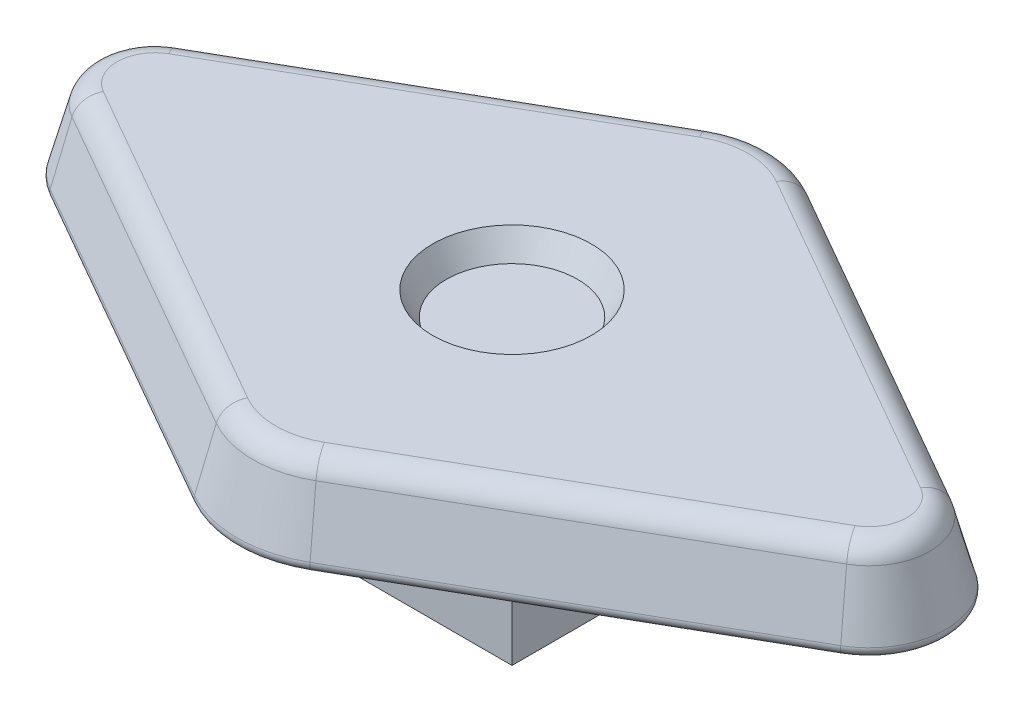
SolidWorks part; units mm, degrees
ref_plane "Front Plane" through (0, 0, 0) normal (0, 0, 1) x (1, 0, 0)
ref_plane "Top Plane" through (0, 0, 0) normal (0, 1, 0) x (1, 0, 0)
ref_plane "Right Plane" through (0, 0, 0) normal (1, 0, 0) x (0, 0, -1)
sketch "Sketch1" plane through (0, 0, 0) normal (0, 1, 0) x (1, 0, 0)
  line L1 (-1.27, -1.27) -> (1.27, -1.27)
  line L2 (-1.27, -1.27) -> (-1.27, 1.27)
  line L3 (-1.27, 1.27) -> (1.27, 1.27)
  line L4 (1.27, -1.27) -> (1.27, 1.27)
  line L5 (-1.27, -1.27) -> (1.27, 1.27) construction
  line L6 (-1.27, 1.27) -> (1.27, -1.27) construction
  point P0 (0, 0)
  dimension "D1" = 2.54
extrude "Boss-Extrude1" add sketch "Sketch1" along normal blind 2.54
sketch "Sketch2" plane through (0, 2.54, 0) normal (0, 1, 0) x (1, 0, 0)
  line L0 (-6.985, 0) -> (6.985, 0) construction
  line L1 (0, -4.445) -> (0, 4.445) construction
  line L2 (6.346, 1.1022) -> (0.9464, 4.1933)
  line L3 (-6.346, 1.1022) -> (-0.9464, 4.1933)
  line L4 (-6.346, -1.1022) -> (-0.9464, -4.1933)
  line L5 (6.346, -1.1022) -> (0.9464, -4.1933)
  arc A0 (-0.9464, 4.1933) -> (0.9464, 4.1933) centre (0, 2.54) cw
  arc A1 (6.346, 1.1022) -> (6.346, -1.1022) centre (5.715, 0) cw
  arc A2 (-6.346, 1.1022) -> (-6.346, -1.1022) centre (-5.715, 0) ccw
  arc A3 (-0.9464, -4.1933) -> (0.9464, -4.1933) centre (0, -2.54) ccw
  point P15 (0, 0)
  dimension "D3" = 1.905
  dimension "D4" = 1.27
  dimension "D1" = 6.985
  dimension "D2" = 4.445
extrude "Boss-Extrude2" add sketch "Sketch2" along normal blind 1.397 draft 15
fillet "Fillet1" radius 0.381 8 edges at (0, 3.937, -4.0707) (3.4602, 3.937, -2.3229) (6.6107, 3.937, 0) (3.4602, 3.937, 2.3229) (0, 3.937, 4.0707) (-3.4602, 3.937, 2.3229) (-6.6107, 3.937, 0) (-3.4602, 3.937, -2.3229)
fillet "Fillet2" radius 0.127 8 edges at (-3.6462, 2.54, -2.6477) (0, 2.54, -4.445) (3.6462, 2.54, -2.6477) (6.985, 2.54, 0) (3.6462, 2.54, 2.6477) (0, 2.54, 4.445) (-3.6462, 2.54, 2.6477) (-6.985, 2.54, 0)
sketch "Sketch3" plane through (0, 3.937, 0) normal (0, 1, 0) x (1, 0, 0)
  circle A0 centre (0, 0) radius 1.27
  dimension "D1" = 2.54
extrude "Cut-Extrude1" cut sketch "Sketch3" against normal blind 0.381 draft 30
